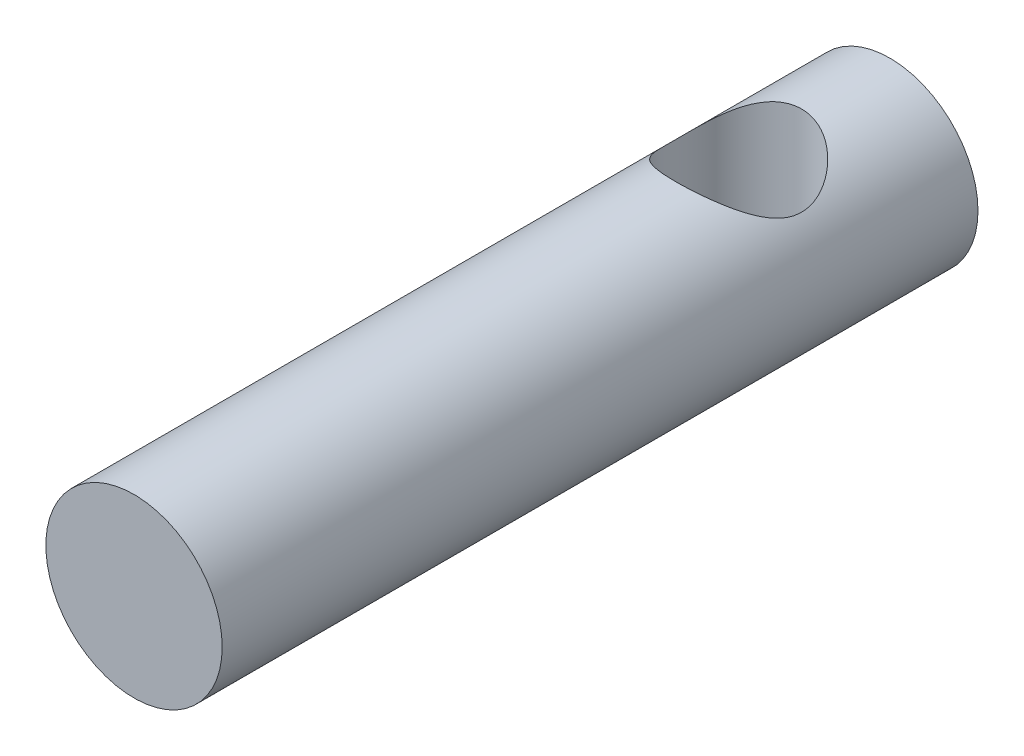
SolidWorks part; units mm, degrees
material "AISI 304"
ref_plane "Front Plane" through (0, 0, 0) normal (0, 0, 1) x (1, 0, 0)
ref_plane "Top Plane" through (0, 0, 0) normal (0, 1, 0) x (1, 0, 0)
ref_plane "Right Plane" through (0, 0, 0) normal (1, 0, 0) x (0, 0, -1)
sketch "Sketch1" plane through (0, 0, 0) normal (0, 0, 1) x (1, 0, 0)
  circle A0 centre (0.6567, 0.6138) radius 1.75
  dimension "D1" = 3.5
extrude "Boss-Extrude1" add sketch "Sketch1" along normal blind 15
sketch "Sketch2" plane through (0, 0, 0) normal (0, 1, 0) x (1, 0, 0)
  line L0 (2.4067, 0) -> (-1.0933, 0) construction
  circle A0 centre (0.6567, -3) radius 1.25
  dimension "D1" = 3
extrude "Cut-Extrude1" cut sketch "Sketch2" against normal through all both and the other way through all
